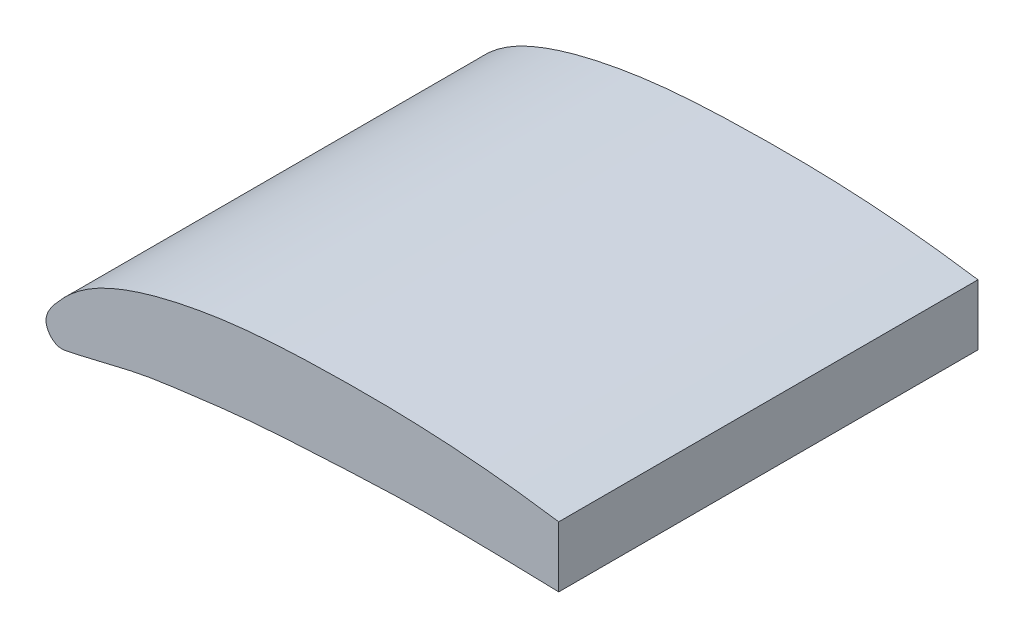
SolidWorks part; units mm, degrees
ref_plane "Front Plane" through (0, 0, 0) normal (0, 0, 1) x (1, 0, 0)
ref_plane "Top Plane" through (0, 0, 0) normal (0, 1, 0) x (1, 0, 0)
ref_plane "Right Plane" through (0, 0, 0) normal (1, 0, 0) x (0, 0, -1)
curve "Curve1"
  spline degree 3 poles (25.4, 0.0889, 0) (24.9755, 0.1879, 0) (24.1284, 0.3854, 0) (22.4316, 0.7474, 0) (20.3056, 1.1527, 0) (17.7661, 1.6728, 0) (15.2225, 2.1285, 0) (12.6828, 2.5208, 0) (10.1333, 2.7153, 0) (7.5886, 2.7177, 0) (5.4641, 2.6194, 0) (3.7724, 2.3478, 0) (2.7142, 2.0863, 0) (1.8702, 1.7836, 0) (1.2225, 1.4719, 0) (0.6864, 1.0854, 0) (0.2512, 0.6226, 0) (-0.1733, 0.0898, 0) (0.2557, -0.4257, 0) (0.7562, -0.3188, 0) (1.2698, -0.1979, 0) (1.905, -0.0426, 0) (2.7433, 0.1487, 0) (3.8055, 0.2872, 0) (5.4925, 0.5064, 0) (7.6119, 0.6227, 0) (10.1512, 0.7472, 0) (12.6929, 0.6952, 0) (15.2354, 0.6324, 0) (17.7755, 0.4534, 0) (20.3173, 0.2785, 0) (22.4335, 0.1017, 0) (24.1313, 0.0327, 0) (24.9769, -0.0484, 0) (25.4, -0.0889, 0) knots 0 0 0 0 0.025045 0.049982 0.099693 0.149405 0.198931 0.248178 0.297011 0.345669 0.394384 0.418982 0.444018 0.456913 0.470405 0.485361 0.494029 0.508284 0.517562 0.523649 0.536105 0.548579 0.561002 0.585562 0.610033 0.658766 0.707435 0.756094 0.804785 0.853571 0.902386 0.951201 0.975578 1 1 1 1
sketch "Sketch1" plane through (0, 0, 0) normal (0, 0, 1) x (1, 0, 0)
  line L0 (25.4, 0.0889) -> (25.4, -0.0889) construction
  line L1 (254, 0.889) -> (254, -0.889)
  line L2 (0, 0) -> (254, 0) construction
  line L3 (127, 0) -> (127, 24.8566) construction
  line L4 (139.7, 0) -> (139.7, 6.6099) construction
  line L5 (139.7, 6.6099) -> (139.7, 23.1662)
  line L6 (50.8, 0) -> (50.8, 4.4198) construction
  line L7 (50.8, 4.4198) -> (50.8, 25.402) construction
  line L8 (101.6, 0) -> (101.6, 7.1792) construction
  line L9 (101.6, 7.1792) -> (101.6, 26.8232) construction
  line L10 (147.4927, 0) -> (147.4927, 6.3416) construction
  line L11 (147.4927, 6.3416) -> (147.4927, 21.9573) construction
  circle A0 centre (50.8, 14.9109) radius 7.9375
  circle A1 centre (101.6, 17.0012) radius 7.9375
  circle A2 centre (147.4927, 14.1494) radius 2.2522
  spline S0 degree 3 poles (801.0896, 2896.6153) (93.9918, -50.1126) (62.4745, -7.7955) (22.4316, 0.7474) (20.3056, 1.1527) (17.7661, 1.6728) (15.2225, 2.1285) (12.6828, 2.5208) (10.1333, 2.7153) (7.5886, 2.7177) (5.4641, 2.6194) (3.7724, 2.3478) (2.7142, 2.0863) (1.8702, 1.7836) (1.2225, 1.4719) (0.6864, 1.0854) (0.2512, 0.6226) (-0.1733, 0.0898) (0.2557, -0.4257) (0.7562, -0.3188) (1.2698, -0.1979) (1.905, -0.0426) (2.7433, 0.1487) (3.8055, 0.2872) (5.4925, 0.5064) (7.6119, 0.6227) (10.1512, 0.7472) (12.6929, 0.6952) (15.2354, 0.6324) (17.7755, 0.4534) (20.3173, 0.2785) (22.4335, 0.1017) (51.136, -1.0652) (75.492, -52.2811) (315.1102, 2985.1217) knots -2.25291 -2.25291 -2.25291 -2.25291 0.025045 0.049982 0.099693 0.149405 0.198931 0.248178 0.297011 0.345669 0.394384 0.418982 0.444018 0.456913 0.470405 0.485361 0.494029 0.508284 0.517562 0.523649 0.536105 0.548579 0.561002 0.585562 0.610033 0.658766 0.707435 0.756094 0.804785 0.853571 0.902386 0.951201 0.975578 2.552608 2.552608 2.552608 2.552608 only from (25.4, 0.0889) to (25.4, -0.0889) construction
  spline S1 degree 3 poles (25.4, 0.0889) (24.9755, 0.1879) (24.1284, 0.3854) (22.4316, 0.7474) (20.3056, 1.1527) (17.7661, 1.6728) (15.2225, 2.1285) (12.6828, 2.5208) (10.1333, 2.7153) (7.5886, 2.7177) (5.4641, 2.6194) (3.7724, 2.3478) (2.7142, 2.0863) (1.8702, 1.7836) (1.2225, 1.4719) (0.6864, 1.0854) (0.2512, 0.6226) (-0.1733, 0.0898) (0.2557, -0.4257) (0.7562, -0.3188) (1.2698, -0.1979) (1.905, -0.0426) (2.7433, 0.1487) (3.8055, 0.2872) (5.4925, 0.5064) (7.6119, 0.6227) (10.1512, 0.7472) (12.6929, 0.6952) (15.2354, 0.6324) (17.7755, 0.4534) (20.3173, 0.2785) (22.4335, 0.1017) (24.1313, 0.0327) (24.9769, -0.0484) (25.4, -0.0889) knots 0 0 0 0 0.025045 0.049982 0.099693 0.149405 0.198931 0.248178 0.297011 0.345669 0.394384 0.418982 0.444018 0.456913 0.470405 0.485361 0.494029 0.508284 0.517562 0.523649 0.536105 0.548579 0.561002 0.585562 0.610033 0.658766 0.707435 0.756094 0.804785 0.853571 0.902386 0.951201 0.975578 1 1 1 1 construction
  spline S2 degree 3 poles (254, 0.889) (249.7553, 1.8786) (241.2842, 3.8535) (224.3158, 7.4736) (203.0565, 11.5272) (177.6613, 16.7283) (152.2253, 21.2846) (126.8284, 25.208) (101.3332, 27.1529) (75.8856, 27.1773) (54.6411, 26.1945) (37.7241, 23.4783) (27.1418, 20.8628) (18.7017, 17.8364) (12.2246, 14.7192) (6.8643, 10.8535) (2.5124, 6.2258) (-1.7329, 0.8975) (2.5571, -4.257) (7.5624, -3.188) (12.6982, -1.9788) (19.0498, -0.4259) (27.4332, 1.4865) (38.0551, 2.8725) (54.9249, 5.0635) (76.1187, 6.227) (101.5119, 7.4722) (126.9288, 6.9519) (152.354, 6.3244) (177.755, 4.534) (203.1733, 2.7851) (224.3353, 1.0168) (241.3134, 0.3266) (249.7685, -0.4836) (254, -0.889) knots 0 0 0 0 0.025045 0.049982 0.099693 0.149405 0.198931 0.248178 0.297011 0.345669 0.394384 0.418982 0.444018 0.456913 0.470405 0.485361 0.494029 0.508284 0.517562 0.523649 0.536105 0.548579 0.561002 0.585562 0.610033 0.658766 0.707435 0.756094 0.804785 0.853571 0.902386 0.951201 0.975578 1 1 1 1
  point P9 (139.7, 0)
  point P12 (50.8, 0)
  point P19 (50.8, 22.8484)
  point P20 (50.8, 6.9734)
  point P21 (101.6, 0)
  point P27 (147.4927, 0)
  dimension "D5" = 15.875
  dimension "D7" = 15.875
  dimension "D1" = 254
  dimension "D2" = 24.8566
  dimension "D3" = 139.7
  dimension "D4" = 50.8
  dimension "D6" = 50.8
  dimension "D8" = 147.4927
extrude "Boss-Extrude1" add sketch "Sketch1" along normal blind 114.3 contours L5 S2 | A0 | A1
